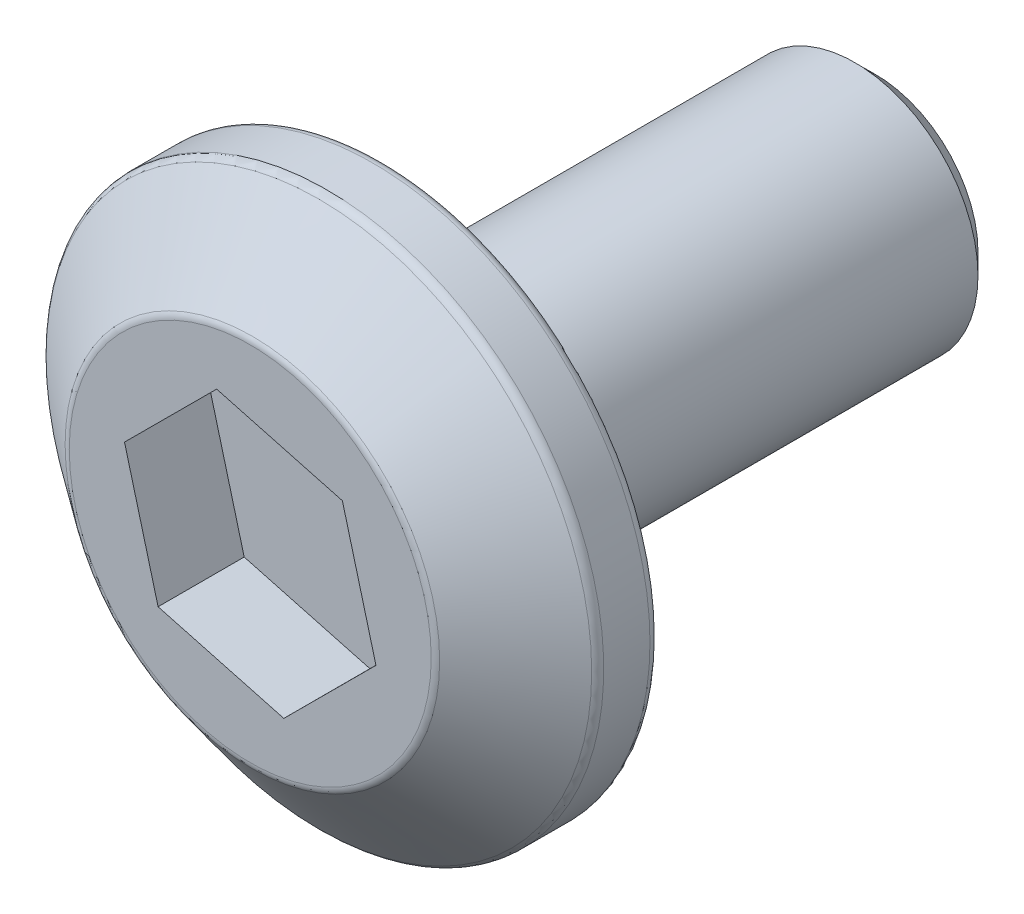
SolidWorks part; units mm, degrees
material "1.0037 (S235JR)"
ref_plane "Front Plane" through (0, 0, 0) normal (0, 0, 1) x (1, 0, 0)
ref_plane "Top Plane" through (0, 0, 0) normal (0, 1, 0) x (1, 0, 0)
ref_plane "Right Plane" through (0, 0, 0) normal (1, 0, 0) x (0, 0, -1)
sketch "Sketch1" plane through (0, 0, 0) normal (0, 0, 1) x (1, 0, 0)
  circle A0 centre (0, 0) radius 3
  dimension "D1" = 6
extrude "Boss-Extrude1" add sketch "Sketch1" along normal blind 12
sketch "Sketch2" plane through (0, 0, 12) normal (0, 0, 1) x (1, 0, 0)
  circle A0 centre (0, 0) radius 6.75
  dimension "D1" = 13.5
extrude "Boss-Extrude2" add sketch "Sketch2" along normal blind 1.5
ref_plane "Plane1" through (0, 0, 15.25) normal (0, 0, 1) x (1, 0, 0)
sketch "Sketch3" plane through (0, 0, 15.25) normal (0, 0, 1) x (1, 0, 0)
  circle A0 centre (0, 0) radius 4.5
  dimension "D1" = 9
loft "Loft1" add profiles "Sketch3" section edge at (6.75, 0, 13.5) section "Sketch3"
fillet "Fillet1" radius 0.25 3 edges at (4.5, 0, 15.25) (6.75, 0, 13.5) (6.75, 0, 12)
sketch "Sketch6" plane through (0, 0, 15.25) normal (0, 0, 1) x (1, 0, 0)
  line L1 (3.0665, -0.8246) -> (2.2474, 2.2433)
  line L2 (2.2474, 2.2433) -> (-0.8191, 3.068)
  line L3 (-0.8191, 3.068) -> (-3.0665, 0.8246)
  line L4 (-3.0665, 0.8246) -> (-2.2474, -2.2433)
  line L5 (-2.2474, -2.2433) -> (0.8191, -3.068)
  line L6 (0.8191, -3.068) -> (3.0665, -0.8246)
  circle A0 centre (0, 0) radius 2.75 construction
  dimension "D1" = 5.5
extrude "Cut-Extrude1" cut sketch "Sketch6" against normal blind 2.1
chamfer "Chamfer2" distance 0.5 angle 45 1 edges at (3, 0, 0)
